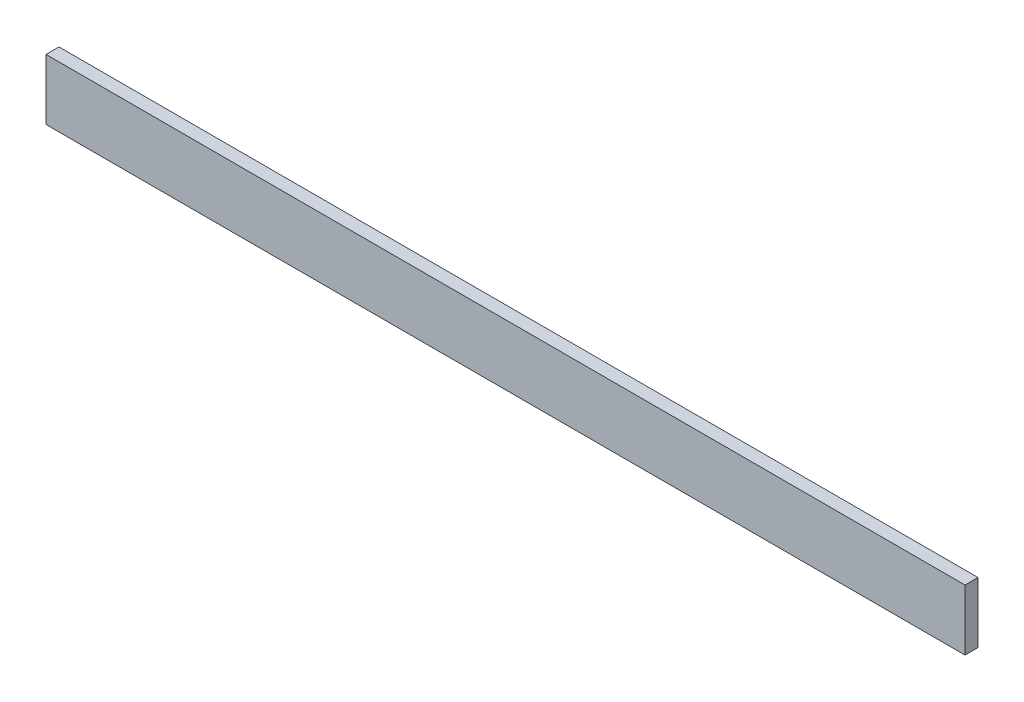
SolidWorks part; units mm, degrees
ref_plane "Front Plane" through (0, 0, 0) normal (0, 0, 1) x (1, 0, 0)
ref_plane "Top Plane" through (0, 0, 0) normal (0, 1, 0) x (1, 0, 0)
ref_plane "Right Plane" through (0, 0, 0) normal (1, 0, 0) x (0, 0, -1)
sketch "Sketch1" plane through (0, 0, 0) normal (0, 0, 1) x (1, 0, 0)
  line L1 (53, 3.5) -> (-53, 3.5)
  line L2 (53, 3.5) -> (53, -3.5)
  line L3 (53, -3.5) -> (-53, -3.5)
  line L4 (-53, 3.5) -> (-53, -3.5)
extrude "Boss-Extrude1" add sketch "Sketch1" along normal blind 1.5
